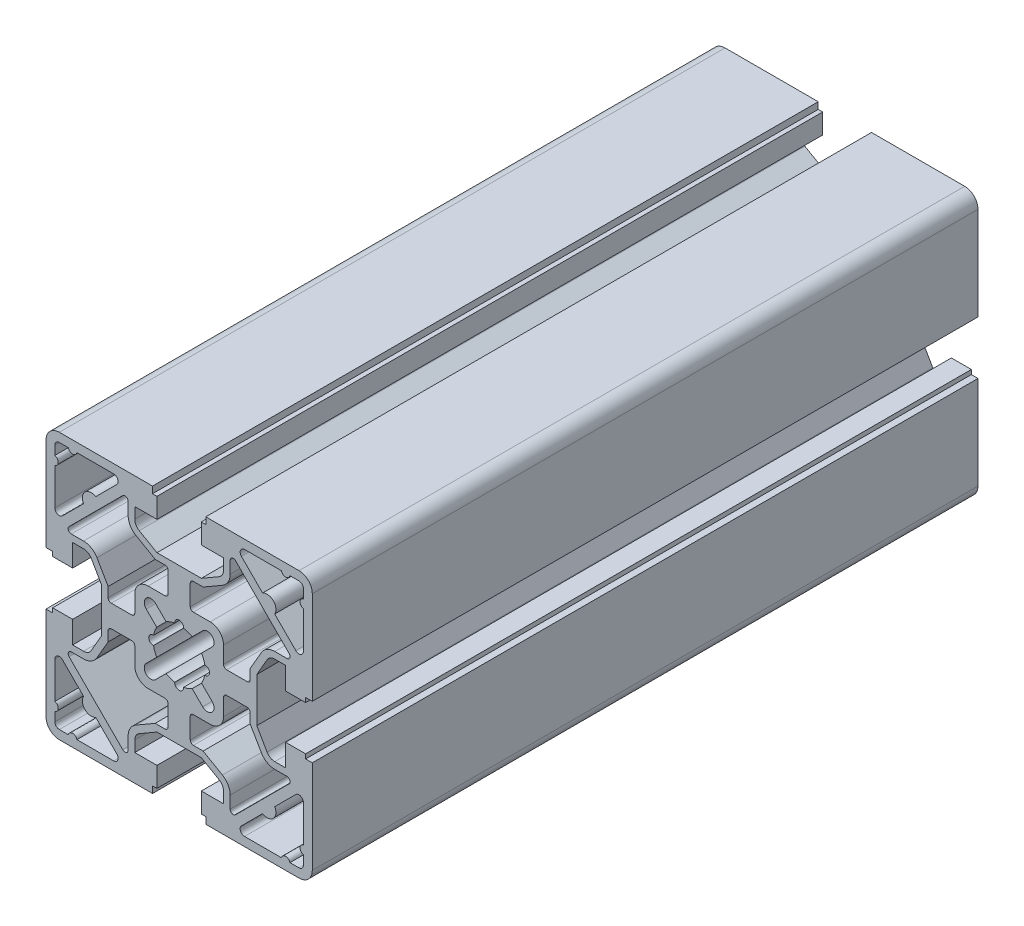
SolidWorks part; units mm, degrees
material "6061-T6 (SS)"
ref_plane "Alzado" through (0, 0, 0) normal (0, 0, 1) x (1, 0, 0)
ref_plane "Planta" through (0, 0, 0) normal (0, 1, 0) x (1, 0, 0)
ref_plane "Vista lateral" through (0, 0, 0) normal (1, 0, 0) x (0, 0, -1)
sketch "Croquis1" plane through (0, 0, 0) normal (0, 0, 1) x (1, 0, 0)
  line L0 (-5, 17.5) -> (5, 17.5)
  line L1 (-30, -30) -> (30, -30) construction
  line L2 (-30, -30) -> (-30, 30) construction
  line L3 (-30, 30) -> (30, 30) construction
  line L4 (30, -30) -> (30, 30) construction
  line L5 (-30, -30) -> (30, 30) construction
  line L6 (-30, 30) -> (30, -30) construction
  line L7 (-7, -10) -> (-3.2, -10)
  line L8 (-10, -7) -> (-10, -3.2)
  line L9 (-7, 10) -> (-3.2, 10)
  line L10 (10, -7) -> (10, -3.2)
  line L11 (-10, -10) -> (10, 10) construction
  line L12 (-10, 10) -> (10, -10) construction
  line L13 (-30, 27) -> (-30, 6)
  line L14 (-30, 6) -> (-28.5, 6)
  line L15 (-28.5, 6) -> (-28.5, 5)
  line L16 (-28.5, 5) -> (-24, 5)
  line L17 (-24, 5) -> (-24, 10)
  line L18 (-24, 10) -> (-21.5415, 10)
  line L19 (-19.8094, 9) -> (-17.5, 5)
  line L20 (-30, 0) -> (30, 0) construction
  line L21 (0, 30) -> (0, -30) construction
  line L22 (-17.5, 5) -> (-17.5, -5)
  line L23 (-9, 19.8094) -> (-5, 17.5)
  line L24 (-10, 24) -> (-10, 21.5415)
  line L25 (-5, 24) -> (-10, 24)
  line L26 (-5, 28.5) -> (-5, 24)
  line L27 (-6, 28.5) -> (-5, 28.5)
  line L28 (-6, 30) -> (-6, 28.5)
  line L29 (-27, 30) -> (-6, 30)
  line L30 (-19.8094, -9) -> (-17.5, -5)
  line L31 (-24, -10) -> (-21.5415, -10)
  line L32 (-24, -5) -> (-24, -10)
  line L33 (-28.5, -5) -> (-24, -5)
  line L34 (-28.5, -6) -> (-28.5, -5)
  line L35 (-30, -6) -> (-28.5, -6)
  line L36 (-30, -27) -> (-30, -6)
  line L37 (-27, -30) -> (-6, -30)
  line L38 (-6, -30) -> (-6, -28.5)
  line L39 (-6, -28.5) -> (-5, -28.5)
  line L40 (-5, -28.5) -> (-5, -24)
  line L41 (-5, -24) -> (-10, -24)
  line L42 (-10, -24) -> (-10, -21.5415)
  line L43 (-9, -19.8094) -> (-5, -17.5)
  line L44 (-5, -17.5) -> (5, -17.5)
  line L45 (9, -19.8094) -> (5, -17.5)
  line L46 (10, -24) -> (10, -21.5415)
  line L47 (5, -24) -> (10, -24)
  line L48 (5, -28.5) -> (5, -24)
  line L49 (6, -28.5) -> (5, -28.5)
  line L50 (6, -30) -> (6, -28.5)
  line L51 (27, -30) -> (6, -30)
  line L52 (30, -27) -> (30, -6)
  line L53 (30, -6) -> (28.5, -6)
  line L54 (28.5, -5) -> (24, -5)
  line L55 (24, -5) -> (24, -10)
  line L56 (24, -10) -> (21.5415, -10)
  line L57 (19.8094, -9) -> (17.5, -5)
  line L58 (17.5, 5) -> (17.5, -5)
  line L59 (19.8094, 9) -> (17.5, 5)
  line L60 (24, 10) -> (21.5415, 10)
  line L61 (24, 5) -> (24, 10)
  line L62 (28.5, 5) -> (24, 5)
  line L63 (28.5, 6) -> (28.5, 5)
  line L64 (30, 6) -> (28.5, 6)
  line L65 (30, 27) -> (30, 6)
  line L66 (27, 30) -> (6, 30)
  line L67 (6, 30) -> (6, 28.5)
  line L68 (6, 28.5) -> (5, 28.5)
  line L69 (5, 28.5) -> (5, 24)
  line L70 (5, 24) -> (10, 24)
  line L71 (10, 24) -> (10, 21.5415)
  line L72 (9, 19.8094) -> (5, 17.5)
  line L73 (-24, 11.5) -> (-21.5415, 11.5)
  line L74 (-18.5104, 9.75) -> (-16, 5.4019)
  line L75 (-16, 5.4019) -> (-16, 3.2)
  line L76 (-18.5104, -9.75) -> (-16, -5.4019)
  line L77 (-24, -11.5) -> (-21.5415, -11.5)
  line L78 (-10.7, 2.5) -> (-15.3, 2.5)
  line L79 (-10.7, -2.5) -> (-15.3, -2.5)
  line L80 (-16, -3.2) -> (-16, -5.4019)
  line L81 (-16, 5.4019) -> (-16, -5.4019) construction
  line L82 (-24, 11.5) -> (-24.3101, 11.5)
  line L83 (-24.805, 12.695) -> (-18.75, 18.75)
  line L84 (-24.805, -12.695) -> (-18.75, -18.75)
  line L85 (-24, -11.5) -> (-24.3101, -11.5)
  line L86 (24.805, -12.695) -> (18.75, -18.75)
  line L87 (24, -11.5) -> (24.3101, -11.5)
  line L88 (24, -11.5) -> (21.5415, -11.5)
  line L89 (18.5104, -9.75) -> (16, -5.4019)
  line L90 (16, -3.2) -> (16, -5.4019)
  line L91 (10.7, -2.5) -> (15.3, -2.5)
  line L92 (10.7, 2.5) -> (15.3, 2.5)
  line L93 (16, 5.4019) -> (16, 3.2)
  line L94 (18.5104, 9.75) -> (16, 5.4019)
  line L95 (24, 11.5) -> (21.5415, 11.5)
  line L96 (24, 11.5) -> (24.3101, 11.5)
  line L97 (24.805, 12.695) -> (18.75, 18.75)
  line L98 (-11.5, -24) -> (-11.5, -21.5415)
  line L99 (-9.75, -18.5104) -> (-5.4019, -16)
  line L100 (-5.4019, -16) -> (-3.2, -16)
  line L101 (9.75, -18.5104) -> (5.4019, -16)
  line L102 (11.5, -24) -> (11.5, -21.5415)
  line L103 (-11.5, -24) -> (-11.5, -24.3101)
  line L104 (-12.695, -24.805) -> (-18.75, -18.75)
  line L105 (12.695, -24.805) -> (18.75, -18.75)
  line L106 (11.5, -24) -> (11.5, -24.3101)
  line L107 (-11.5, 24) -> (-11.5, 21.5415)
  line L108 (-9.75, 18.5104) -> (-5.4019, 16)
  line L109 (-5.4019, 16) -> (-3.2, 16)
  line L110 (9.75, 18.5104) -> (5.4019, 16)
  line L111 (11.5, 24) -> (11.5, 21.5415)
  line L112 (11.5, 24) -> (11.5, 24.3101)
  line L113 (12.695, 24.805) -> (18.75, 18.75)
  line L114 (-11.5, 24) -> (-11.5, 24.3101)
  line L115 (-12.695, 24.805) -> (-18.75, 18.75)
  line L116 (2.5, 15.3) -> (2.5, 10.7)
  line L117 (2.5, -10.7) -> (2.5, -15.3)
  line L118 (-2.5, -10.7) -> (-2.5, -15.3)
  line L119 (-2.5, 15.3) -> (-2.5, 10.7)
  line L120 (-12.3284, 28) -> (-28, 12.3284) construction
  line L121 (-28, 12.3284) -> (-28, 28) construction
  line L122 (-28, 28) -> (-12.3284, 28) construction
  line L123 (-18.7949, 21.5335) -> (-14.0355, 26.2929)
  line L124 (-14.7426, 28) -> (-23.0318, 28)
  line L125 (-24.9682, 28) -> (-27, 28)
  line L126 (-21.5335, 18.7949) -> (-26.2929, 14.0355)
  line L127 (-28, 14.7426) -> (-28, 23.0318)
  line L128 (-28, 24.9682) -> (-28, 27)
  line L129 (18.7949, 21.5335) -> (14.0355, 26.2929)
  line L130 (14.7426, 28) -> (23.0318, 28)
  line L131 (24.9682, 28) -> (27, 28)
  line L132 (28, 24.9682) -> (28, 27)
  line L133 (28, 14.7426) -> (28, 23.0318)
  line L134 (21.5335, 18.7949) -> (26.2929, 14.0355)
  line L135 (21.5335, -18.7949) -> (26.2929, -14.0355)
  line L136 (28, -14.7426) -> (28, -23.0318)
  line L137 (28, -24.9682) -> (28, -27)
  line L138 (24.9682, -28) -> (27, -28)
  line L139 (14.7426, -28) -> (23.0318, -28)
  line L140 (18.7949, -21.5335) -> (14.0355, -26.2929)
  line L141 (-18.7949, -21.5335) -> (-14.0355, -26.2929)
  line L142 (-14.7426, -28) -> (-23.0318, -28)
  line L143 (-24.9682, -28) -> (-27, -28)
  line L144 (-28, -24.9682) -> (-28, -27)
  line L145 (-28, -14.7426) -> (-28, -23.0318)
  line L146 (-21.5335, -18.7949) -> (-26.2929, -14.0355)
  line L147 (3.2, 16) -> (5.4019, 16)
  line L148 (-5.4019, 16) -> (5.4019, 16) construction
  line L149 (3.2, -16) -> (5.4019, -16)
  line L150 (-5.4019, -16) -> (5.4019, -16) construction
  line L151 (28.5, -6) -> (28.5, -5)
  line L152 (-10, 3.2) -> (-10, 7)
  line L153 (3.2, -10) -> (7, -10)
  line L154 (10, 3.2) -> (10, 7)
  line L155 (3.2, 10) -> (7, 10)
  line L156 (0, -5.85) -> (0, 5.85) construction
  line L157 (-1, -5.85) -> (-1, 5.85)
  line L158 (1, -5.85) -> (1, 5.85)
  line L159 (-5.85, 0) -> (5.85, 0) construction
  line L160 (-5.85, 1) -> (5.85, 1)
  line L161 (-5.85, -1) -> (5.85, -1)
  line L162 (-6.364, -6.364) -> (6.364, 6.364) construction
  line L163 (-7.4246, -5.3033) -> (5.3033, 7.4246)
  line L164 (-5.3033, -7.4246) -> (7.4246, 5.3033)
  line L165 (6.364, -6.364) -> (-6.364, 6.364) construction
  line L166 (5.3033, -7.4246) -> (-7.4246, 5.3033)
  line L167 (7.4246, -5.3033) -> (-5.3033, 7.4246)
  circle A0 centre (0, 0) radius 5.85
  arc A1 (30, 27) -> (27, 30) centre (27, 27) ccw
  arc A2 (-30, -27) -> (-27, -30) centre (-27, -27) ccw
  arc A3 (27, -30) -> (30, -27) centre (27, -27) ccw
  arc A4 (-27, 30) -> (-30, 27) centre (-27, 27) ccw
  arc A5 (-9, 19.8094) -> (-10, 21.5415) centre (-8, 21.5415) cw
  arc A6 (10, 21.5415) -> (9, 19.8094) centre (8, 21.5415) cw
  arc A7 (19.8094, 9) -> (21.5415, 10) centre (21.5415, 8) cw
  arc A8 (21.5415, -10) -> (19.8094, -9) centre (21.5415, -8) cw
  arc A9 (9, -19.8094) -> (10, -21.5415) centre (8, -21.5415) cw
  arc A10 (-10, -21.5415) -> (-9, -19.8094) centre (-8, -21.5415) cw
  arc A11 (-19.8094, -9) -> (-21.5415, -10) centre (-21.5415, -8) cw
  arc A12 (-21.5415, 10) -> (-19.8094, 9) centre (-21.5415, 8) cw
  arc A13 (-7, -10) -> (-10, -7) centre (-7, -7) cw
  arc A14 (7, 10) -> (10, 7) centre (7, 7) cw
  arc A15 (7, -10) -> (10, -7) centre (7, -7) ccw
  arc A16 (-10, 7) -> (-7, 10) centre (-7, 7) cw
  arc A17 (-21.5415, 11.5) -> (-18.5104, 9.75) centre (-21.5415, 8) cw
  arc A18 (-18.5104, -9.75) -> (-21.5415, -11.5) centre (-21.5415, -8) cw
  arc A19 (18.5104, -9.75) -> (21.5415, -11.5) centre (21.5415, -8) ccw
  arc A20 (21.5415, 11.5) -> (18.5104, 9.75) centre (21.5415, 8) ccw
  arc A21 (-11.5, -21.5415) -> (-9.75, -18.5104) centre (-8, -21.5415) cw
  arc A22 (9.75, -18.5104) -> (11.5, -21.5415) centre (8, -21.5415) cw
  arc A23 (-9.75, 18.5104) -> (-11.5, 21.5415) centre (-8, 21.5415) cw
  arc A24 (11.5, 21.5415) -> (9.75, 18.5104) centre (8, 21.5415) cw
  arc A25 (-21.5335, 18.7949) -> (-18.7949, 21.5335) centre (-19.8107, 19.8107) cw
  arc A26 (-23.0318, 28) -> (-24.9682, 28) centre (-24, 28.25) cw
  arc A27 (-28, 23.0318) -> (-28, 24.9682) centre (-28.25, 24) ccw
  arc A28 (23.0318, 28) -> (24.9682, 28) centre (24, 28.25) ccw
  arc A29 (28, 23.0318) -> (28, 24.9682) centre (28.25, 24) cw
  arc A30 (18.7949, 21.5335) -> (21.5335, 18.7949) centre (19.8107, 19.8107) cw
  arc A31 (28, -23.0318) -> (28, -24.9682) centre (28.25, -24) ccw
  arc A32 (23.0318, -28) -> (24.9682, -28) centre (24, -28.25) cw
  arc A33 (21.5335, -18.7949) -> (18.7949, -21.5335) centre (19.8107, -19.8107) cw
  arc A34 (-23.0318, -28) -> (-24.9682, -28) centre (-24, -28.25) ccw
  arc A35 (-28, -23.0318) -> (-28, -24.9682) centre (-28.25, -24) cw
  arc A36 (-18.7949, -21.5335) -> (-21.5335, -18.7949) centre (-19.8107, -19.8107) cw
  arc A37 (-1, -5.85) -> (1, -5.85) centre (0, -5.85) ccw
  arc A38 (1, 5.85) -> (-1, 5.85) centre (0, 5.85) ccw
  arc A39 (-5.85, 1) -> (-5.85, -1) centre (-5.85, 0) ccw
  arc A40 (5.85, -1) -> (5.85, 1) centre (5.85, 0) ccw
  arc A41 (-7.4246, -5.3033) -> (-5.3033, -7.4246) centre (-6.364, -6.364) ccw
  arc A42 (7.4246, 5.3033) -> (5.3033, 7.4246) centre (6.364, 6.364) ccw
  arc A43 (5.3033, -7.4246) -> (7.4246, -5.3033) centre (6.364, -6.364) ccw
  arc A44 (-5.3033, 7.4246) -> (-7.4246, 5.3033) centre (-6.364, 6.364) ccw
  arc A45 (14.0355, 26.2929) -> (14.7426, 28) centre (14.7426, 27) cw
  arc A46 (28, 14.7426) -> (26.2929, 14.0355) centre (27, 14.7426) cw
  arc A47 (27, 28) -> (28, 27) centre (27, 27) cw
  arc A48 (28, -27) -> (27, -28) centre (27, -27) cw
  arc A49 (26.2929, -14.0355) -> (28, -14.7426) centre (27, -14.7426) cw
  arc A50 (14.7426, -28) -> (14.0355, -26.2929) centre (14.7426, -27) cw
  arc A51 (-14.0355, -26.2929) -> (-14.7426, -28) centre (-14.7426, -27) cw
  arc A52 (-27, -28) -> (-28, -27) centre (-27, -27) cw
  arc A53 (-28, -14.7426) -> (-26.2929, -14.0355) centre (-27, -14.7426) cw
  arc A54 (-14.0355, 26.2929) -> (-14.7426, 28) centre (-14.7426, 27) ccw
  arc A55 (-27, 28) -> (-28, 27) centre (-27, 27) ccw
  arc A56 (-26.2929, 14.0355) -> (-28, 14.7426) centre (-27, 14.7426) cw
  arc A57 (24.3101, 11.5) -> (24.805, 12.695) centre (24.3101, 12.2) ccw
  arc A58 (11.5, 24.3101) -> (12.695, 24.805) centre (12.2, 24.3101) cw
  arc A59 (2.5, 15.3) -> (3.2, 16) centre (3.2, 15.3) cw
  arc A60 (2.5, 10.7) -> (3.2, 10) centre (3.2, 10.7) ccw
  arc A61 (15.3, 2.5) -> (16, 3.2) centre (15.3, 3.2) ccw
  arc A62 (10.7, 2.5) -> (10, 3.2) centre (10.7, 3.2) cw
  arc A63 (2.5, -15.3) -> (3.2, -16) centre (3.2, -15.3) ccw
  arc A64 (2.5, -10.7) -> (3.2, -10) centre (3.2, -10.7) cw
  arc A65 (16, -3.2) -> (15.3, -2.5) centre (15.3, -3.2) ccw
  arc A66 (10.7, -2.5) -> (10, -3.2) centre (10.7, -3.2) ccw
  arc A67 (24.805, -12.695) -> (24.3101, -11.5) centre (24.3101, -12.2) ccw
  arc A68 (12.695, -24.805) -> (11.5, -24.3101) centre (12.2, -24.3101) cw
  arc A69 (-24.805, -12.695) -> (-24.3101, -11.5) centre (-24.3101, -12.2) cw
  arc A70 (-11.5, -24.3101) -> (-12.695, -24.805) centre (-12.2, -24.3101) cw
  arc A71 (-2.5, -15.3) -> (-3.2, -16) centre (-3.2, -15.3) cw
  arc A72 (-2.5, -10.7) -> (-3.2, -10) centre (-3.2, -10.7) ccw
  arc A73 (-15.3, -2.5) -> (-16, -3.2) centre (-15.3, -3.2) ccw
  arc A74 (-10.7, -2.5) -> (-10, -3.2) centre (-10.7, -3.2) cw
  arc A75 (-15.3, 2.5) -> (-16, 3.2) centre (-15.3, 3.2) cw
  arc A76 (-10.7, 2.5) -> (-10, 3.2) centre (-10.7, 3.2) ccw
  arc A77 (-2.5, 10.7) -> (-3.2, 10) centre (-3.2, 10.7) cw
  arc A78 (-2.5, 15.3) -> (-3.2, 16) centre (-3.2, 15.3) ccw
  arc A79 (-11.5, 24.3101) -> (-12.695, 24.805) centre (-12.2, 24.3101) ccw
  arc A80 (-24.3101, 11.5) -> (-24.805, 12.695) centre (-24.3101, 12.2) cw
  point P0 (0, 0)
  point P33 (-17.5, 0)
  point P48 (0, -17.5)
  point P75 (0, 17.5)
  point P92 (-10, 20.3868)
  point P95 (10, 20.3868)
  point P98 (20.3868, 10)
  point P101 (20.3868, -10)
  point P104 (10, -20.3868)
  point P107 (-10, -20.3868)
  point P110 (-20.3868, -10)
  point P113 (-20.3868, 10)
  point P205 (0, 0)
  point P242 (0, 0)
  point P249 (0, 0)
  point P256 (0, 0)
  point P263 (0, 0)
  point P297 (26, 11.5)
  point P300 (11.5, 26)
  point P303 (2.5, 16)
  point P306 (2.5, 10)
  point P309 (16, 2.5)
  point P312 (10, 2.5)
  point P315 (2.5, -16)
  point P318 (2.5, -10)
  point P321 (16, -2.5)
  point P324 (10, -2.5)
  point P327 (26, -11.5)
  point P330 (11.5, -26)
  point P333 (-26, -11.5)
  point P336 (-11.5, -26)
  point P339 (-2.5, -16)
  point P342 (-2.5, -10)
  point P345 (-16, -2.5)
  point P348 (-10, -2.5)
  point P351 (-16, 2.5)
  point P354 (-10, 2.5)
  point P357 (-2.5, 10)
  point P360 (-2.5, 16)
  point P363 (-11.5, 26)
  point P366 (-26, 11.5)
  dimension "D3" = 11.7
  dimension "D11" = 3
  dimension "D12" = 3
  dimension "D13" = 3
  dimension "D14" = 3
  dimension "D15" = 2
  dimension "D16" = 2
  dimension "D17" = 2
  dimension "D18" = 2
  dimension "D19" = 2
  dimension "D20" = 2
  dimension "D21" = 2
  dimension "D22" = 2
  dimension "D24" = 3
  dimension "D25" = 3
  dimension "D26" = 3
  dimension "D27" = 3
  dimension "D39" = 2
  dimension "D41" = 1
  dimension "D50" = 1
  dimension "D51" = 1
  dimension "D52" = 1
  dimension "D53" = 1
  dimension "D54" = 1
  dimension "D55" = 1
  dimension "D56" = 1
  dimension "D57" = 1
  dimension "D58" = 1
  dimension "D59" = 1
  dimension "D60" = 1
  dimension "D61" = 1
  dimension "D62" = 0.7
  dimension "D63" = 0.7
  dimension "D64" = 0.7
  dimension "D65" = 0.7
  dimension "D66" = 0.7
  dimension "D67" = 0.7
  dimension "D68" = 0.7
  dimension "D69" = 0.7
  dimension "D70" = 0.7
  dimension "D71" = 0.7
  dimension "D72" = 0.7
  dimension "D73" = 0.7
  dimension "D74" = 0.7
  dimension "D75" = 0.7
  dimension "D76" = 0.7
  dimension "D77" = 0.7
  dimension "D78" = 0.7
  dimension "D79" = 0.7
  dimension "D80" = 0.7
  dimension "D81" = 0.7
  dimension "D82" = 0.7
  dimension "D83" = 0.7
  dimension "D84" = 0.7
  dimension "D85" = 0.7
  dimension "D1" = 60
  dimension "D2" = 1.5
  dimension "D4" = 20
  dimension "D5" = 10
  dimension "D6" = 12
  dimension "D7" = 20
  dimension "D8" = 12.5
  dimension "D9" = 6
  dimension "D10" = 30
  dimension "D23" = 20
  dimension "D28" = 1.5
  dimension "D29" = 5
  dimension "D30" = 2
  dimension "D31" = 1.5
  dimension "D32" = 2
  dimension "D34" = 2
  dimension "D35" = 2
  dimension "D36" = 5
  dimension "D37" = 2
  dimension "D38" = 2
  dimension "D40" = 0.5
  dimension "D42" = 0.25
  dimension "D44" = 2
  dimension "D45" = 2
  dimension "D46" = 3
  dimension "D47" = 18
  dimension "D48" = 18
  dimension "D49" = 3
  dimension "D33" = 1.5
  dimension "D43" = 4
extrude "Saliente-Extruir1" add sketch "Croquis1" along normal mid plane 150 contours L18 A12 L19 L22 L30 A11 L31 L32 L33 L34 L35 L36 A2 L37 L38 L39 L40 L41 L42 A10 L43 L44 L45 A9 L46 L47 L48 L49 L50 L51 A3 L52 L53 L151 L54 L55 L56 A8 L57 L58 L59 A7 L60 L61 L62 L63 L64 L65 A1 L66 L67
sketch "Croquis2" [suppressed] plane through (0, 0, 0) normal (1, 0, 0) x (0, 0, -1)
  line L0 (1000, 0) -> (0, 0) construction
  line L1 (1000, 5) -> (1000, -5) construction
  dimension "D1" = 1000
hole_wizard "Taladro de margen para M81" [suppressed] positions "Croquis3" profile "Croquis4" hole size "M8" standard "ISO"
sketch "Croquis3" plane through (30, 0, 0) normal (1, 0, 0) x (0, 0, -1)
  point P0 (0, 0)
  point P3 (-250, 0)
  point P5 (-500, 0)
  dimension "D1" = 250
  dimension "D2" = 250
sketch "Croquis4" plane through (30, 0, 0) normal (0, 1, 0) x (0, 0, -1)
  line L0 (0, 0) -> (0, 60)
  line L1 (0, 60) -> (4.5, 60)
  line L2 (4.5, 60) -> (4.5, 0)
  line L5 (4.5, 0) -> (0, 0)
  line L11 (0, -6.35) -> (0, 107.95) construction
  dimension "Diámetro de taladro hasta el siguiente" = 9
  dimension "Profundidad de taladro hasta el siguiente" = 60
hole_wizard "Taladro de margen para M82" positions "Croquis5" profile "Croquis6" hole size "M8" standard "ISO" end condition through all
sketch "Croquis5" plane through (0, 30, 0) normal (0, 1, 0) x (1, 0, 0)
  line L0 (-1000, 0) -> (49000, 0) construction
  point P0 (0, 40)
  point P9 (0, -40)
  dimension "D1" = 80
sketch "Croquis6" plane through (0, 30, -40) normal (1, 0, 0) x (0, 0, 1)
  line L0 (0, 0) -> (0, 60)
  line L1 (0, 60) -> (4.2, 60)
  line L2 (4.2, 60) -> (4.2, 0)
  line L5 (4.2, 0) -> (0, 0)
  line L11 (0, -6.35) -> (0, 107.95) construction
  dimension "Diámetro de taladro hasta el siguiente" = 8.4
  dimension "Profundidad de taladro hasta el siguiente" = 60
